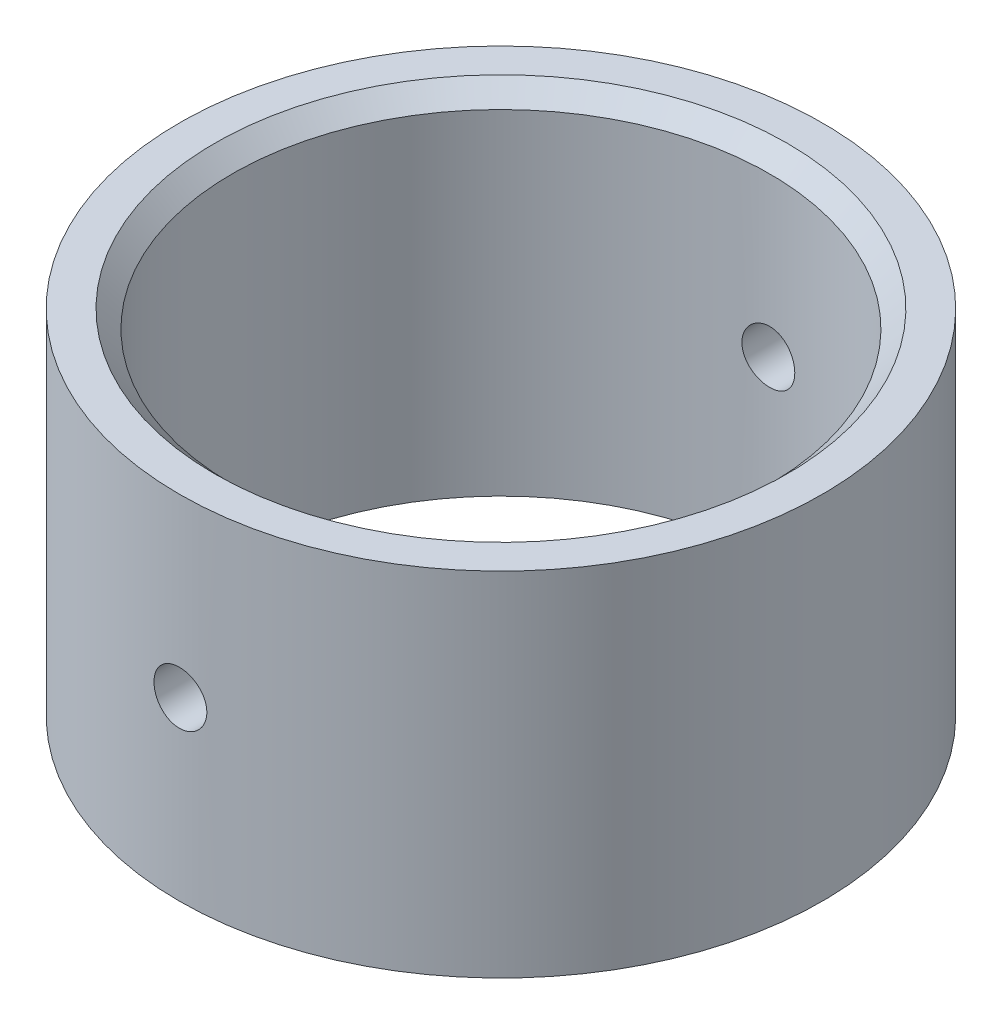
SolidWorks part; units mm, degrees
ref_plane "Front Plane" through (0, 0, 0) normal (0, 0, 1) x (1, 0, 0)
ref_plane "Top Plane" through (0, 0, 0) normal (0, 1, 0) x (1, 0, 0)
ref_plane "Right Plane" through (0, 0, 0) normal (1, 0, 0) x (0, 0, -1)
sketch "Sketch1" plane through (0, 0, 0) normal (0, 1, 0) x (1, 0, 0)
  circle A0 centre (0, 0) radius 15.25
  circle A1 centre (0, 0) radius 18.25
  dimension "D1" = 30.5
  dimension "D2" = 3
extrude "Boss-Extrude1" add sketch "Sketch1" along normal blind 20
sketch "Sketch2" plane through (0, 0, 0) normal (0, 0, 1) x (1, 0, 0)
  line L0 (-18.25, 10) -> (18.25, 10) construction
  line L1 (-18.25, 20) -> (-18.25, 0) construction
  line L2 (18.25, 0) -> (18.25, 20) construction
  circle A0 centre (0, 10) radius 1.5
  dimension "D1" = 3
extrude "Cut-Extrude1" cut sketch "Sketch2" against normal through all both and the other way through all
chamfer "Chamfer1" distance 1 angle 45 1 edges at (0, 20, 15.25)
